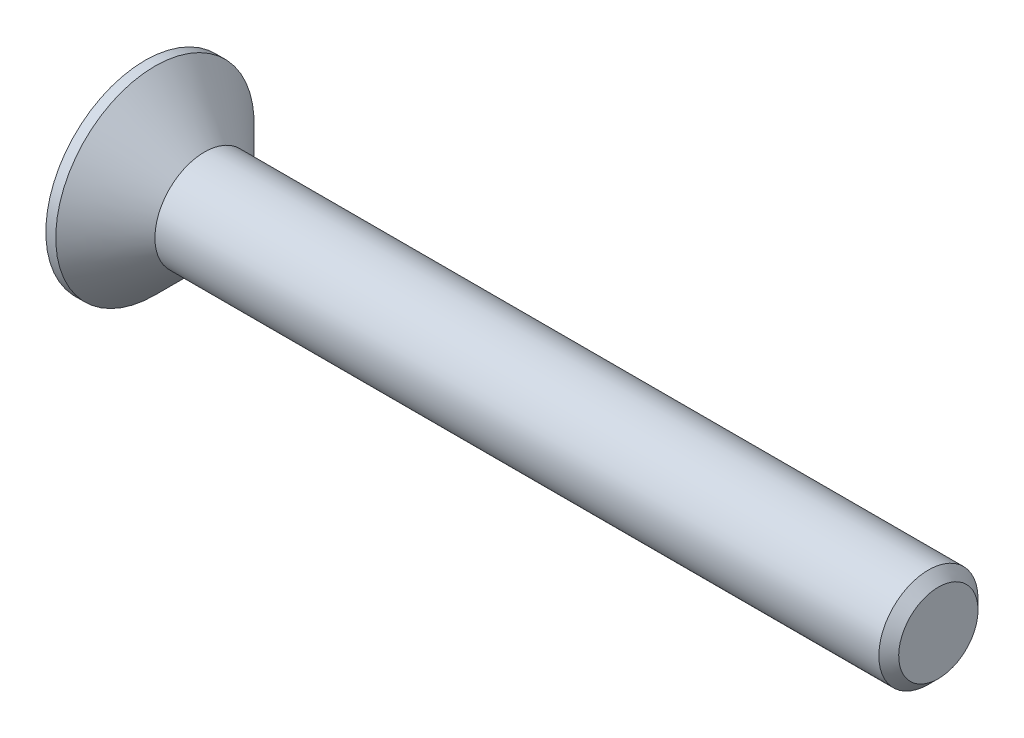
SolidWorks part; units mm, degrees
ref_plane "Front Plane" through (0, 0, 0) normal (0, 0, 1) x (1, 0, 0)
ref_plane "Top Plane" through (0, 0, 0) normal (0, 1, 0) x (1, 0, 0)
ref_plane "Right Plane" through (0, 0, 0) normal (1, 0, 0) x (0, 0, -1)
sketch "Sketch1" plane through (0, 0, 0) normal (0, 0, 1) x (1, 0, 0)
  line L0 (0, 1) -> (-1, 2)
  line L1 (-1, 2) -> (-1.2, 2)
  line L2 (-1.2, 2) -> (-1.2, 0)
  line L3 (-1.2, 0) -> (14.8, 0)
  line L4 (14.8, 0) -> (14.8, 1)
  line L5 (14.8, 1) -> (0, 1)
  dimension "D1" = 1
  dimension "D2" = 16
  dimension "D3" = 45
  dimension "D4" = 2
  dimension "D5" = 1.2
revolve "Revolve1" add sketch "Sketch1" angle 360 about L3
chamfer "Chamfer1" distance 0.2 angle 45 1 edges at (14.8, -1, 0)
sketch "Sketch2" plane through (-1.2, 0, 0) normal (-1, 0, 0) x (0, 0, 1)
  line L1 (-0.7506, 0) -> (-0.3753, -0.65)
  line L2 (-0.3753, -0.65) -> (0.3753, -0.65)
  line L3 (0.3753, -0.65) -> (0.7506, 0)
  line L4 (0.7506, 0) -> (0.3753, 0.65)
  line L5 (0.3753, 0.65) -> (-0.3753, 0.65)
  line L6 (-0.3753, 0.65) -> (-0.7506, 0)
  circle A0 centre (0, 0) radius 0.65 construction
  dimension "D1" = 1.3
extrude "Cut-Extrude1" cut sketch "Sketch2" against normal blind 0.75
